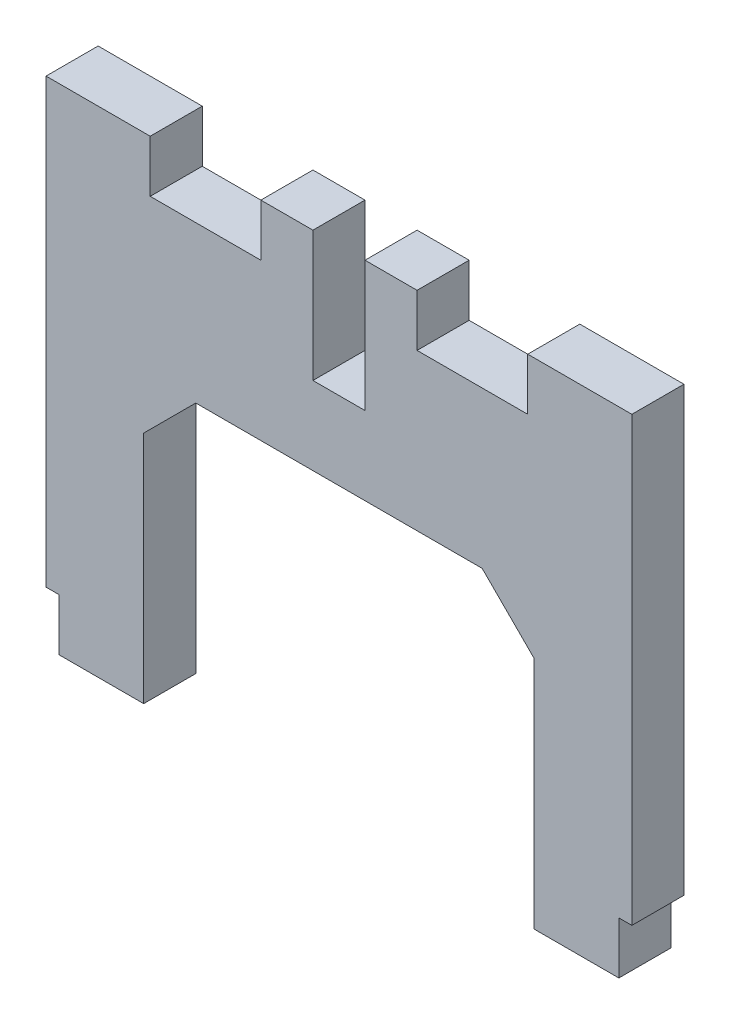
SolidWorks part; units mm, degrees
ref_plane "Front Plane" through (0, 0, 0) normal (0, 0, 1) x (1, 0, 0)
ref_plane "Top Plane" through (0, 0, 0) normal (0, 1, 0) x (1, 0, 0)
ref_plane "Right Plane" through (0, 0, 0) normal (1, 0, 0) x (0, 0, -1)
sketch "Sketch1" plane through (0, 0, 0) normal (0, 0, 1) x (1, 0, 0)
  line L0 (0, 0) -> (0, 30)
  line L1 (0, 30) -> (-20.5, 30)
  line L2 (-20.5, 30) -> (-20.5, 24)
  line L3 (-20.5, 24) -> (-22.5, 24)
  line L9 (-22.5, 18) -> (-7.5, 18)
  line L10 (-7.5, 18) -> (-7.5, -4)
  line L11 (-7.5, -4) -> (-1, -4)
  line L12 (-1, -4) -> (-1, 0)
  line L13 (-1, 0) -> (0, 0)
  line L14 (-22.5, 24) -> (-22.5, 18)
  point P13 (-21.5, 24)
  dimension "D1" = 1
  dimension "D2" = 6.5
  dimension "D3" = 4
  dimension "D4" = 24
  dimension "D5" = 30
  dimension "D6" = 12
  dimension "D7" = 22.5
  dimension "D9" = 20.5
extrude "Boss-Extrude1" add sketch "Sketch1" along normal blind 4
chamfer "Chamfer2" distance 4 angle 45 1 edges at (-7.5, 18, 2)
mirror "Mirror1" about plane through (-22.5, 24, 4) normal (1, 0, 0) of "Chamfer2", "Boss-Extrude1"
sketch "Sketch2" plane through (0, 0, 4) normal (0, 0, 1) x (1, 0, 0)
  line L1 (-24.5, 30) -> (-28.5, 30)
  line L2 (-24.5, 30) -> (-24.5, 34)
  line L3 (-24.5, 34) -> (-28.5, 34)
  line L4 (-28.5, 30) -> (-28.5, 34)
  line L5 (-20.5, 30) -> (-16.5, 30)
  line L6 (-20.5, 30) -> (-20.5, 34)
  line L7 (-20.5, 34) -> (-16.5, 34)
  line L8 (-16.5, 30) -> (-16.5, 34)
  line L9 (0, 30) -> (-8, 30)
  line L10 (0, 30) -> (0, 34)
  line L11 (0, 34) -> (-8, 34)
  line L12 (-8, 30) -> (-8, 34)
  line L13 (-45, 30) -> (-37, 30)
  line L14 (-45, 30) -> (-45, 34)
  line L15 (-45, 34) -> (-37, 34)
  line L16 (-37, 30) -> (-37, 34)
  dimension "D1" = 4
  dimension "D2" = 4
  dimension "D3" = 4
  dimension "D4" = 8
  dimension "D5" = 8
extrude "Boss-Extrude2" add sketch "Sketch2" against normal up to surface (4 mm away) up to face at (-22.5, 12, 0)
